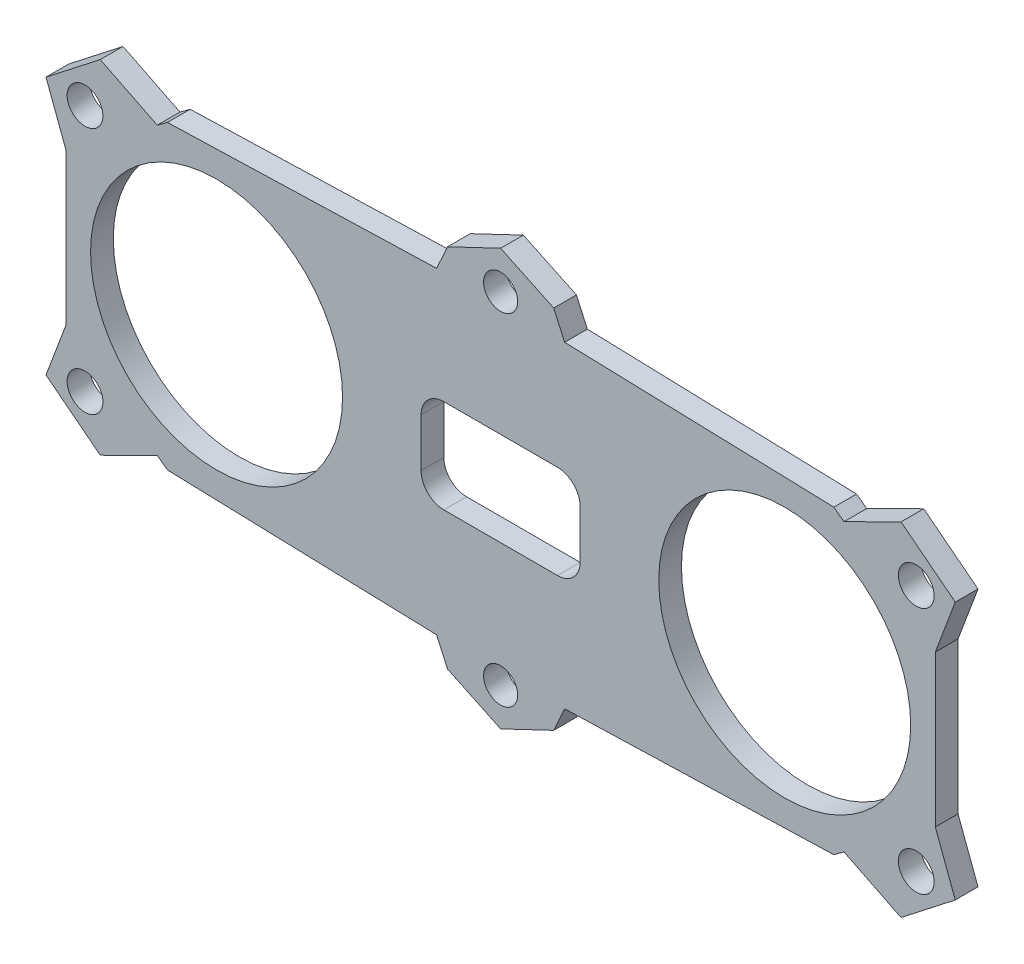
SolidWorks part; units mm, degrees
ref_plane "Front Plane" through (0, 0, 0) normal (0, 0, 1) x (1, 0, 0)
ref_plane "Top Plane" through (0, 0, 0) normal (0, 1, 0) x (1, 0, 0)
ref_plane "Right Plane" through (0, 0, 0) normal (1, 0, 0) x (0, 0, -1)
sketch "Sketch1" plane through (0, 0, 0) normal (0, 0, 1) x (1, 0, 0)
  line L0 (0, 36.6328) -> (-9.3396, 32.1848)
  line L1 (-9.3396, 32.1848) -> (-11.2637, 27.9309)
  line L2 (-11.2637, 27.9309) -> (-58.6462, 26.4903)
  line L3 (-58.6462, 26.4903) -> (-76.5, 13.3359)
  line L4 (-76.5, 13.3359) -> (-76.5, -13.3359)
  line L5 (-87.0431, 0) -> (20.0163, 0) construction
  line L6 (0, 32.2788) -> (0, 0) construction
  line L7 (76.5, 13.3359) -> (76.5, -13.3359)
  line L8 (58.6462, 26.4903) -> (76.5, 13.3359)
  line L9 (11.2637, 27.9309) -> (58.6462, 26.4903)
  line L10 (9.3396, 32.1848) -> (11.2637, 27.9309)
  line L11 (0, 36.6328) -> (9.3396, 32.1848)
  line L12 (0, -36.6328) -> (9.3396, -32.1848)
  line L13 (9.3396, -32.1848) -> (11.2637, -27.9309)
  line L14 (11.2637, -27.9309) -> (58.6462, -26.4903)
  line L15 (58.6462, -26.4903) -> (76.5, -13.3359)
  line L16 (-58.6462, -26.4903) -> (-76.5, -13.3359)
  line L17 (-11.2637, -27.9309) -> (-58.6462, -26.4903)
  line L18 (-9.3396, -32.1848) -> (-11.2637, -27.9309)
  line L19 (0, -36.6328) -> (-9.3396, -32.1848)
  circle A0 centre (0, 30) radius 3
  circle A1 centre (-50, 0) radius 22.175
  circle A2 centre (50, 0) radius 22.175
  circle A3 centre (0, -30) radius 3
  point P35 (76.5, 0)
  point P36 (-76.5, 0)
  dimension "D1" = 6
  dimension "D2" = 44.35
  dimension "D3" = 60
  dimension "D4" = 100
  dimension "D5" = 153
extrude "Boss-Extrude1" add sketch "Sketch1" along normal blind 4
sketch "Sketch2" plane through (0, 0, 4) normal (0, 0, 1) x (1, 0, 0)
  line L1 (10, 8.25) -> (-10, 8.25)
  line L2 (14, 4.25) -> (14, -4.25)
  line L3 (10, -8.25) -> (-10, -8.25)
  line L4 (-14, 4.25) -> (-14, -4.25)
  line L5 (14, 8.25) -> (-14, -8.25) construction
  line L6 (14, -8.25) -> (-14, 8.25) construction
  arc A1 (10, 8.25) -> (14, 4.25) centre (10, 4.25) cw
  arc A2 (14, -4.25) -> (10, -8.25) centre (10, -4.25) cw
  arc A3 (-10, -8.25) -> (-14, -4.25) centre (-10, -4.25) cw
  arc A4 (-10, 8.25) -> (-14, 4.25) centre (-10, 4.25) ccw
  point P0 (0, 0)
  dimension "D1" = 4
  dimension "D2" = 28
  dimension "D3" = 16.5
extrude "Cut-Extrude1" cut sketch "Sketch2" against normal through all
sketch "Sketch3" plane through (0, 0, 4) normal (0, 0, 1) x (1, 0, 0)
  line L0 (-60.4361, 25.1715) -> (-70.4704, 30.1559)
  line L1 (-58.6462, 26.4903) -> (-76.5, 13.3359) construction
  line L2 (-70.4704, 30.1559) -> (-80.0188, 22.702)
  line L3 (-80.0188, 22.702) -> (-76.5, 13.3359)
  line L4 (-76.5, 13.3359) -> (-60.4361, 25.1715)
  line L5 (0, 0) -> (0, 46.5274) construction
  line L6 (76.5, 13.3359) -> (60.4361, 25.1715)
  line L7 (80.0188, 22.702) -> (76.5, 13.3359)
  line L8 (70.4704, 30.1559) -> (80.0188, 22.702)
  line L9 (60.4361, 25.1715) -> (70.4704, 30.1559)
  line L10 (0, 0) -> (-26.0239, 0) construction
  line L11 (60.4361, -25.1715) -> (70.4704, -30.1559)
  line L12 (70.4704, -30.1559) -> (80.0188, -22.702)
  line L13 (80.0188, -22.702) -> (76.5, -13.3359)
  line L14 (76.5, -13.3359) -> (60.4361, -25.1715)
  line L15 (-76.5, -13.3359) -> (-60.4361, -25.1715)
  line L16 (-80.0188, -22.702) -> (-76.5, -13.3359)
  line L17 (-70.4704, -30.1559) -> (-80.0188, -22.702)
  line L18 (-60.4361, -25.1715) -> (-70.4704, -30.1559)
  circle A0 centre (-73.15, 21.8) radius 3.15
  circle A1 centre (73.15, 21.8) radius 3.15
  circle A2 centre (-73.15, -21.8) radius 3.15
  circle A3 centre (73.15, -21.8) radius 3.15
  point P22 (-73.1622, 21.7973)
  dimension "D1" = 6.3
  dimension "D2" = 73.15
  dimension "D3" = 21.8
extrude "Boss-Extrude2" add sketch "Sketch3" against normal up to surface (4 mm away) up to face at (0, 0, 0)
